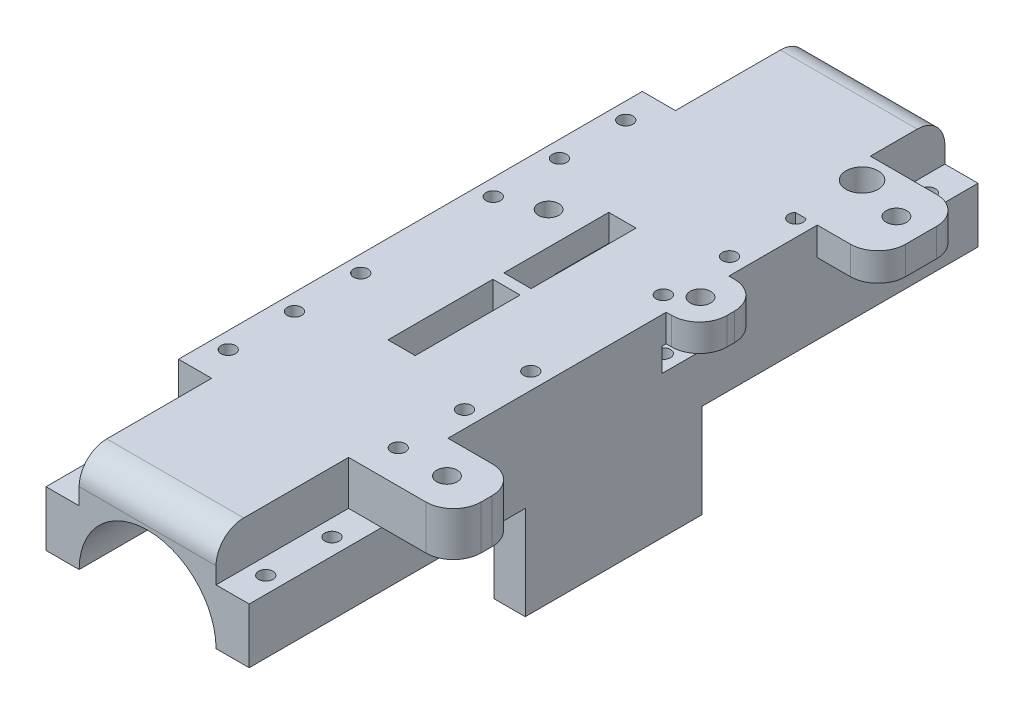
SolidWorks part; units mm, degrees
ref_plane "Plan de face" through (0, 0, 0) normal (0, 0, 1) x (1, 0, 0)
ref_plane "Plan de dessus" through (0, 0, 0) normal (0, 1, 0) x (1, 0, 0)
ref_plane "Plan de droite" through (0, 0, 0) normal (1, 0, 0) x (0, 0, -1)
sketch "Esquisse1" plane through (0, 0, 0) normal (0, 0, 1) x (1, 0, 0)
  line L0 (0, 0) -> (-84.6745, 0) construction
  line L1 (0, 0) -> (94.0931, 0) construction
  line L2 (-12.4, 0) -> (-18.4, 0)
  line L3 (0, 0) -> (0, 12.4) construction
  line L4 (-18.4, 0) -> (-18.4, 18)
  line L5 (-18.4, 18) -> (18.4, 18)
  line L6 (18.4, 0) -> (18.4, 18)
  line L7 (12.4, 0) -> (18.4, 0)
  line L8 (0, 12.4) -> (0, 18) construction
  arc A0 (-12.4, 0) -> (12.4, 0) centre (0, 0) cw
  point P11 (0, 18)
  dimension "D1" = 6
  dimension "D2" = 18
extrude "Boss.-Extru.1" add sketch "Esquisse1" along normal blind 132
sketch "Esquisse3" plane through (0, 18, 0) normal (0, -1, 0) x (1, 0, 0)
  line L0 (-18.4, 66) -> (18.4, 66) construction
  line L3 (0, 66) -> (0, 73.4675) construction
  line L4 (-18.4, 132) -> (-18.4, 0) construction
  line L5 (2.4701, 46) -> (-2.4701, 46)
  line L6 (2.4701, 46) -> (2.4701, 86)
  line L7 (2.4701, 86) -> (-2.4701, 86)
  line L8 (-2.4701, 46) -> (-2.4701, 86)
  line L9 (2.4701, 46) -> (-2.4701, 86) construction
  line L10 (2.4701, 86) -> (-2.4701, 46) construction
  dimension "D1" = 40
extrude "Enlèv. mat.-Extru.2" cut sketch "Esquisse3" along normal blind 9
sketch "Esquisse4" plane through (0, 18, 0) normal (0, 1, 0) x (1, 0, 0)
  line L0 (18.4, -12) -> (-19.7679, -12) construction
  line L1 (0, 0) -> (0, -28.5028) construction
  line L2 (15.4, 0) -> (15.4, -28.5028) construction
  line L3 (18.4, -6) -> (-18.4211, -6) construction
  line L4 (18.4, 0) -> (-18.4, 0) construction
  line L5 (18.4, -132) -> (18.4, 0) construction
  line L6 (18.4, -66) -> (-18.4, -66) construction
  line L7 (-18.4, -132) -> (-18.4, 0) construction
  circle A0 centre (15.4, -6) radius 1.3
  circle A1 centre (15.4, -18) radius 1.3
  circle A2 centre (-15.4, -6) radius 1.3
  circle A3 centre (-15.4, -18) radius 1.3
  circle A4 centre (15.4, -30) radius 1.3
  circle A5 centre (-15.4, -30) radius 1.3
  circle A6 centre (15.4, -42) radius 1.3
  circle A7 centre (-15.4, -42) radius 1.3
  circle A8 centre (15.4, -54) radius 1.3
  circle A9 centre (-15.4, -54) radius 1.3
  circle A10 centre (-15.4, -126) radius 1.3
  circle A11 centre (-15.4, -114) radius 1.3
  circle A12 centre (-15.4, -102) radius 1.3
  circle A13 centre (-15.4, -90) radius 1.3
  circle A14 centre (-15.4, -78) radius 1.3
  circle A15 centre (15.4, -78) radius 1.3
  circle A16 centre (15.4, -90) radius 1.3
  circle A17 centre (15.4, -102) radius 1.3
  circle A18 centre (15.4, -114) radius 1.3
  circle A19 centre (15.4, -126) radius 1.3
  dimension "D1" = 3
  dimension "D2" = 6
  dimension "D3" = 6
  dimension "D4" = 5
extrude "Enlèv. mat.-Extru.3" cut sketch "Esquisse4" against normal blind 18
sketch "Esquisse5" plane through (0, 18, 0) normal (0, 1, 0) x (1, 0, 0)
  line L0 (0, 0) -> (0, -132) construction
  line L1 (18.4, 0) -> (12.4, 0)
  line L2 (18.4, 0) -> (18.4, -24)
  line L3 (18.4, -24) -> (12.4, -24)
  line L4 (12.4, 0) -> (12.4, -24)
  line L5 (18.4, 0) -> (-18.4, 0) construction
  line L6 (18.4, -132) -> (-18.4, -132) construction
  line L7 (18.4, -66) -> (-18.4, -66) construction
  line L8 (18.4, -132) -> (18.4, 0) construction
  line L9 (-18.4, -132) -> (-18.4, 0) construction
  line L10 (-18.4, -132) -> (-12.4, -132)
  line L11 (-12.4, -132) -> (-12.4, -108)
  line L12 (-18.4, -108) -> (-12.4, -108)
  line L13 (-18.4, -132) -> (-18.4, -108)
  line L14 (-18.4, 0) -> (-18.4, -24)
  line L15 (-18.4, -24) -> (-12.4, -24)
  line L16 (-12.4, 0) -> (-12.4, -24)
  line L17 (-18.4, 0) -> (-12.4, 0)
  line L18 (12.4, -132) -> (12.4, -108)
  line L19 (18.4, -108) -> (12.4, -108)
  line L20 (18.4, -132) -> (18.4, -108)
  line L21 (18.4, -132) -> (12.4, -132)
  dimension "D1" = 24
  dimension "D2" = 6
extrude "Enlèv. mat.-Extru.4" cut sketch "Esquisse5" against normal blind 8
sketch "Esquisse7" plane through (-18.4, 0, 0) normal (-1, 0, 0) x (0, 0, 1)
  line L0 (66, 18) -> (66, 0) construction
  line L1 (108, 18) -> (24, 18) construction
  line L2 (132, 0) -> (0, 0) construction
  line L4 (65, 0) -> (67, 0)
  line L5 (65, 0) -> (65, 18)
  line L6 (65, 18) -> (67, 18)
  line L7 (67, 0) -> (67, 18)
  line L8 (65, 0) -> (67, 18) construction
  line L9 (65, 18) -> (67, 0) construction
  point P6 (66, 9)
  dimension "D1" = 2
extrude "Boss.-Extru.2" add sketch "Esquisse7" against normal through all
sketch "Esquisse8" plane through (0, 0, 65) normal (0, 0, -1) x (-1, 0, 0)
  line L0 (0, 0) -> (16.5032, 0) construction
  line L1 (-12.4, 0) -> (12.4, 0) construction
  line L2 (0, 0) -> (-16.5316, 0) construction
  line L3 (12.775, 0) -> (-12.775, 0)
  arc A0 (12.775, 0) -> (-12.775, 0) centre (0, 0) ccw
extrude "Enlèv. mat.-Extru.5" cut sketch "Esquisse8" along normal blind 15
sketch "Esquisse9" plane through (0, 0, 67) normal (0, 0, 1) x (1, 0, 0)
  line L0 (0, 0) -> (13.8492, 0) construction
  line L1 (12.4, 0) -> (-12.4, 0) construction
  line L2 (0, 0) -> (-14.6616, 0) construction
  line L3 (12.775, 0) -> (-12.775, 0)
  arc A0 (12.775, 0) -> (-12.775, 0) centre (0, 0) ccw
extrude "Enlèv. mat.-Extru.6" cut sketch "Esquisse9" along normal blind 15
sketch "Esquisse10" plane through (0, 0, 0) normal (0, -1, 0) x (1, 0, 0)
  line L0 (12.775, 82) -> (18.4, 82)
  line L1 (18.4, 132) -> (18.4, 0) construction
  line L2 (12.775, 50) -> (18.4, 50)
  line L3 (18.4, 50) -> (18.4, 82)
  line L4 (12.775, 82) -> (12.775, 50)
  line L5 (0, 67) -> (0, 64.9415) construction
  line L6 (12.775, 67) -> (-12.775, 67) construction
  line L7 (-12.775, 50) -> (-18.4, 50)
  line L8 (-18.4, 50) -> (-18.4, 82)
  line L9 (-12.775, 82) -> (-12.775, 50)
  line L10 (-12.775, 82) -> (-18.4, 82)
extrude "Boss.-Extru.3" add sketch "Esquisse10" along normal blind 17
sketch "Esquisse12" plane through (18.4, 0, 0) normal (1, 0, 0) x (0, 0, -1)
  line L1 (-108, 18) -> (-96, 18)
  line L2 (-108, 18) -> (-108, 10)
  line L3 (-108, 10) -> (-96, 10)
  line L4 (-96, 18) -> (-96, 10)
  dimension "D1" = 8
  dimension "D2" = 12
extrude "Boss.-Extru.4" add sketch "Esquisse12" along normal blind 13
sketch "Esquisse14" plane through (18.4, 0, 0) normal (1, 0, 0) x (0, 0, -1)
  line L0 (-96, 18) -> (-24, 18) construction
  line L1 (-56.4694, 18) -> (-45.1194, 18)
  line L2 (-56.4694, 18) -> (-56.4694, 10.412)
  line L3 (-56.4694, 10.412) -> (-45.1194, 10.412)
  line L4 (-45.1194, 18) -> (-45.1194, 10.412)
extrude "Boss.-Extru.5" add sketch "Esquisse14" along normal blind 6
sketch "Esquisse16" plane through (24.4, 0, 0) normal (1, 0, 0) x (0, 0, -1)
  line L1 (-43.9372, 13.05) -> (-57.196, 13.05)
  line L2 (-43.9372, 13.05) -> (-43.9372, 8.7778)
  line L3 (-43.9372, 8.7778) -> (-57.196, 8.7778)
  line L4 (-57.196, 13.05) -> (-57.196, 8.7778)
extrude "Enlèv. mat.-Extru.7" cut sketch "Esquisse16" against normal blind 11
sketch "Esquisse17" plane through (18.4, 0, 0) normal (1, 0, 0) x (0, 0, -1)
  line L0 (-45.1194, 18) -> (-24, 18) construction
  line L1 (-29.1148, 18) -> (-13.5015, 18)
  line L2 (-29.1148, 18) -> (-29.1148, 12.8991)
  line L3 (-29.1148, 12.8991) -> (-13.5015, 12.8991)
  line L4 (-13.5015, 18) -> (-13.5015, 12.8991)
extrude "Boss.-Extru.6" add sketch "Esquisse17" along normal blind 11 and the other way blind 11
sketch "Esquisse11" plane through (0, 18, 0) normal (0, 1, 0) x (1, 0, 0)
  line L0 (-18.4, -66) -> (18.5601, -66) construction
  line L1 (-18.4, -108) -> (-18.4, -24) construction
  line L2 (15.4, -6) -> (15.4, -18) construction
  line L3 (-35.4042, -116) -> (36.1198, -116) construction
  line L4 (-37.228, -16) -> (37.9436, -16) construction
  line L5 (0, -132) -> (0, 0) construction
  line L6 (26.63, -116) -> (26.63, -16) construction
  line L7 (-26.63, -116) -> (-26.63, -16) construction
  line L8 (12.4, -132) -> (-12.4, -132) construction
  line L9 (12.4, 0) -> (-12.4, 0) construction
  line L10 (24.22, -116) -> (24.22, -16) construction
  line L11 (26.63, -102) -> (-26.63, -102) construction
  line L12 (19.13, -116) -> (19.13, -16) construction
  line L13 (-26.63, -51) -> (26.63, -51) construction
  line L14 (26.63, -20.6) -> (-26.63, -20.6) construction
  line L15 (-8.37, -116) -> (-8.37, -16) construction
  circle A0 centre (24.22, -102) radius 1.85
  circle A1 centre (19.13, -51) radius 1.85
  circle A2 centre (24.22, -20.6) radius 1.85
  circle A3 centre (-8.37, -51) radius 1.85
  circle A4 centre (15.4, -6) radius 1.3
  circle A5 centre (15.4, -18) radius 2.9164
  dimension "D8" = 65
  dimension "D9" = 4.6
  dimension "D10" = 35
  dimension "D1" = 50
  dimension "D2" = 50
  dimension "D3" = 26.63
  dimension "D4" = 26.63
  dimension "D5" = 2.41
  dimension "D6" = 14
  dimension "D7" = 7.5
extrude "Enlèv. mat.-Extru.8" cut sketch "Esquisse11" against normal blind 8
fillet "Congé1" radius 5 6 edges at (29.4, 15.4496, 13.5015) (24.4, 15.525, 45.1194) (24.4, 15.525, 56.4694) (31.4, 14, 96) (31.4, 14, 108) (29.4, 15.4496, 29.1148)
sketch "Esquisse18" plane through (-2.4701, 0, 0) normal (1, 0, 0) x (0, 0, -1)
  line L1 (-55.739, 13.14) -> (-46.0613, 13.14)
  line L2 (-55.739, 13.14) -> (-55.739, 4.8868)
  line L3 (-55.739, 4.8868) -> (-46.0613, 4.8868)
  line L4 (-46.0613, 13.14) -> (-46.0613, 4.8868)
extrude "Enlèv. mat.-Extru.9" cut sketch "Esquisse18" against normal blind 10
fillet "Congé2" radius 5 2 edges at (0, 18, 0) (0, 18, 132)
